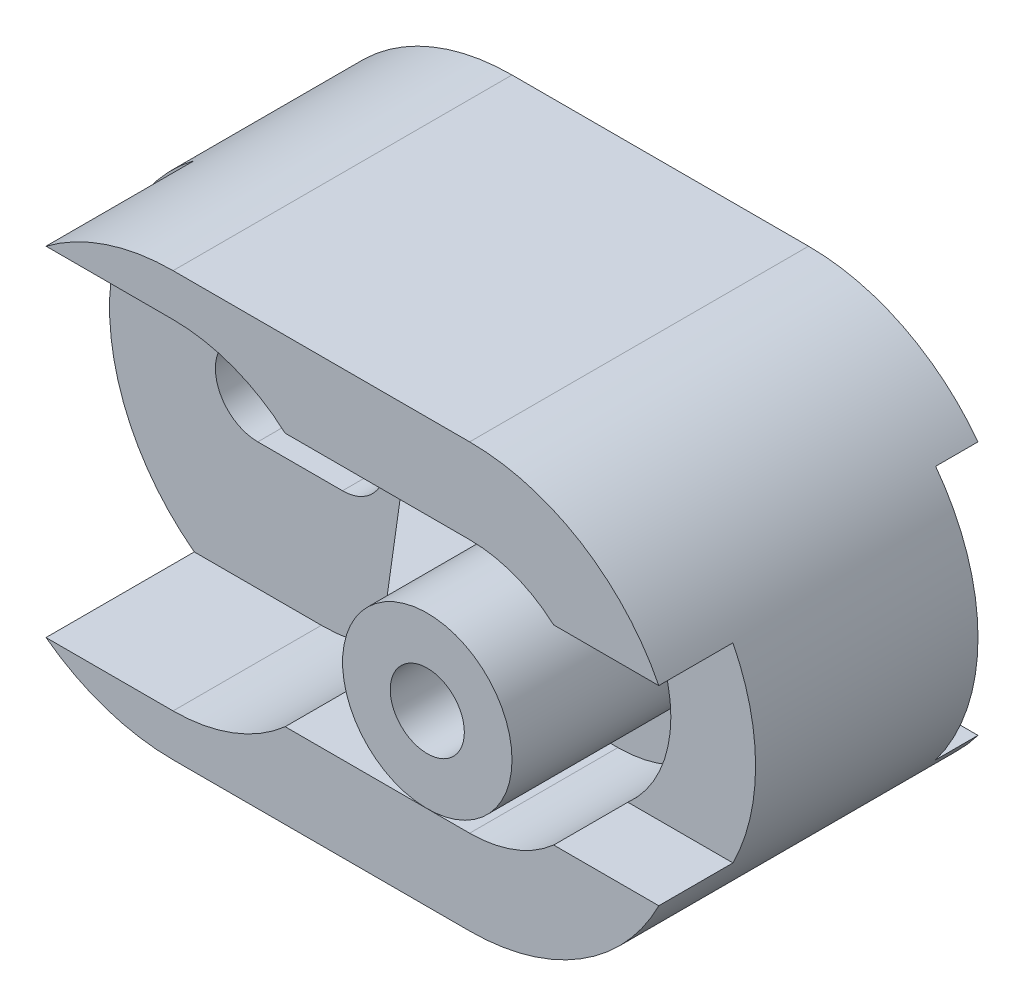
SolidWorks part; units mm, degrees
ref_plane "Front" through (0, 0, 0) normal (0, 0, 1) x (1, 0, 0)
ref_plane "Top" through (0, 0, 0) normal (0, 1, 0) x (1, 0, 0)
ref_plane "Right" through (0, 0, 0) normal (1, 0, 0) x (0, 0, -1)
sketch "Sketch1" plane through (0, 0, 0) normal (0, 0, 1) x (1, 0, 0)
  line L0 (-3.5, 0) -> (3.5, 0) construction
  line L1 (-3.5, 5) -> (3.5, 5)
  line L2 (-3.5, -5) -> (3.5, -5)
  arc A0 (-3.5, 5) -> (-3.5, -5) centre (-3.5, 0) ccw
  arc A1 (3.5, -5) -> (3.5, 5) centre (3.5, 0) ccw
  point P3 (0, 0)
  dimension "D3" = 5
  dimension "D1" = 7
  dimension "D2" = 0
extrude "Boss-Extrude1" add sketch "Sketch1" along normal blind 8
sketch "Sketch2" plane through (0, 0, 0) normal (1, 0, 0) x (0, 0, -1)
  line L0 (0, -5) -> (0, 5) construction
  line L1 (0, 3) -> (-1, 3)
  line L2 (0, 3) -> (0, -3)
  line L3 (0, -3) -> (-1, -3)
  line L4 (-1, 3) -> (-1, -3)
  line L5 (-8, 5) -> (0, 5) construction
  line L6 (-8, -5) -> (0, -5) construction
  dimension "D1" = 1
  dimension "D2" = 2
  dimension "D3" = 2
extrude "Cut-Extrude1" cut sketch "Sketch2" against normal mid plane 18
sketch "Sketch3" plane through (0, 0, 1) normal (0, 0, -1) x (-1, 0, 0)
  line L0 (3.0009, 0) -> (8.5, 0) construction
  line L1 (3.0009, 2) -> (8.5, 2)
  line L2 (3.0009, -2) -> (8.5, -2)
  arc A0 (7.5, -3) -> (7.5, 3) centre (3.5, 0) ccw construction
  arc A1 (3.0009, 2) -> (3.0009, -2) centre (3.0009, 0) ccw
  arc A2 (8.5, -2) -> (8.5, 2) centre (8.5, 0) ccw
  point P5 (5.7505, 0)
  dimension "D1" = 2
extrude "Cut-Extrude2" cut sketch "Sketch3" against normal blind 1
sketch "Sketch4" plane through (0, 0, 8) normal (0, 0, 1) x (1, 0, 0)
  line L0 (-9.1616, 0) -> (-3.5, 0) construction
  line L1 (-9.1616, 4) -> (-3.5, 4)
  line L2 (-9.1616, -4) -> (-3.5, -4)
  line L3 (-3.5, 0) -> (3.5, 0) construction
  line L4 (-3.5, 3) -> (3.5, 3)
  line L5 (-3.5, -3) -> (3.5, -3)
  arc A0 (-9.1616, 4) -> (-9.1616, -4) centre (-9.1616, 0) ccw
  arc A1 (-3.5, -4) -> (-3.5, 4) centre (-3.5, 0) ccw
  arc A2 (-3.5, 3) -> (-3.5, -3) centre (-3.5, 0) ccw
  arc A3 (3.5, -3) -> (3.5, 3) centre (3.5, 0) ccw
  circle A4 centre (3.5, 0) radius 2
  point P3 (-6.3308, 0)
  point P10 (0, 0)
  arc M5 (-3.5, 5) -> (-3.5, -5) centre (-3.5, 0) ccw
  dimension "D1" = 4
  dimension "D4" = 3
  dimension "D5" = 4
  dimension "D2" = 3.5
  dimension "D3" = 7
extrude "Cut-Extrude3" cut sketch "Sketch4" against normal blind 3.5 contours L1 A0 L2 M5 | A2 L4 A1 L1 L2 L5 M5 | L4 A2 L5 A1 | L5 A3 L4 A1
sketch "Sketch5" plane through (0, 0, 0) normal (0, 1, 0) x (1, 0, 0)
  line L0 (1.5, -8) -> (-1.5, -4.5)
  line L1 (1.5, -8) -> (5.5, -8) construction
  line L2 (-1.5, -4.5) -> (1.5, -4.5)
  line L3 (1.5, -4.5) -> (1.5, -8)
  dimension "D1" = 3
  dimension "D2" = 3.5
extrude "Boss-Extrude3" add sketch "Sketch5" along normal mid plane 1 separate body
sketch "Sketch6" plane through (0, 0, 2) normal (0, 0, -1) x (-1, 0, 0)
  line L0 (3.0009, 0) -> (5.0009, 0) construction
  line L1 (3.0009, 1) -> (5.0009, 1)
  line L2 (3.0009, -1) -> (5.0009, -1)
  arc A0 (3.0009, 1) -> (3.0009, -1) centre (3.0009, 0) ccw
  arc A1 (5.0009, -1) -> (5.0009, 1) centre (5.0009, 0) ccw
  point P4 (4.0009, 0)
  dimension "D2" = 1
  dimension "D1" = 2
extrude "Cut-Extrude4" cut sketch "Sketch6" against normal blind 6.0257
sketch "Sketch7" plane through (0, 0, 8) normal (0, 0, 1) x (1, 0, 0)
  line L5 (5.4843, 2.25) -> (7.9651, 2.25)
  line L7 (5.4843, -2.25) -> (7.9651, -2.25)
  line L10 (-3.5, -4) -> (-6.5, -4)
  line L11 (-3.5, -5) -> (3.5, -5)
  line L12 (3.5, 5) -> (-3.5, 5)
  line L13 (-6.5, 4) -> (-3.5, 4)
  line L14 (-0.8542, 3) -> (3.5, 3)
  line L15 (3.5, -3) -> (-0.8542, -3)
  line L16 (-3.5, -4) -> (-6.5, -4)
  line L17 (-3.5, -5) -> (3.5, -5)
  line L18 (3.5, 5) -> (-3.5, 5)
  line L19 (-6.5, 4) -> (-3.5, 4)
  line L20 (-0.8542, 3) -> (3.5, 3)
  line L21 (3.5, -3) -> (-0.8542, -3)
  arc A7 (-6.5, -4) -> (-3.5, -5) centre (-3.5, 0) ccw
  arc A8 (3.5, -5) -> (3.5, 5) centre (3.5, 0) ccw
  arc A9 (-3.5, 5) -> (-6.5, 4) centre (-3.5, 0) ccw
  arc A10 (-0.8542, 3) -> (-3.5, 4) centre (-3.5, 0) ccw
  arc A11 (3.5, -3) -> (3.5, 3) centre (3.5, 0) ccw
  arc A12 (-3.5, -4) -> (-0.8542, -3) centre (-3.5, 0) ccw
  arc A13 (-6.5, -4) -> (-3.5, -5) centre (-3.5, 0) ccw
  arc A14 (3.5, -5) -> (3.5, 5) centre (3.5, 0) ccw
  arc A15 (-3.5, 5) -> (-6.5, 4) centre (-3.5, 0) ccw
  arc A16 (-0.8542, 3) -> (-3.5, 4) centre (-3.5, 0) ccw
  arc A17 (3.5, -3) -> (3.5, 3) centre (3.5, 0) ccw
  arc A18 (-3.5, -4) -> (-0.8542, -3) centre (-3.5, 0) ccw
  arc M18 (3.5, -5) -> (3.5, 5) centre (3.5, 0) ccw
  arc M24 (3.5, 3) -> (3.5, -3) centre (3.5, 0) cw
  dimension "D1" = 0
  dimension "D2" = 2.75
  dimension "D3" = 4.5
extrude "Cut-Extrude5" cut sketch "Sketch7" against normal blind 1.75 contours L7 L5 M24 M18
sketch "Sketch8" plane through (0, 0, 8) normal (0, 0, 1) x (1, 0, 0)
  circle A1 centre (3.5, 0) radius 2
  circle A2 centre (3.5, 0) radius 2
  dimension "D1" = 0
extrude "Boss-Extrude4" add sketch "Sketch8" along normal blind 1
hole_wizard "M2.2x0.45 Tapped Hole1" positions "3DSketch1" profile "Sketch9" tap size "M2.2x0.45" standard "ISO"
sketch3d "3DSketch1"
  line L0 (3.5, 0, 4.5) -> (3.5, 0, 9) construction
  point P0 (3.5, 0, 9)
sketch "Sketch9" plane through (3.5, 0, 9) normal (1, 0, 0) x (0, -1, 0)
  line L0 (0, 0) -> (0, 5.0258)
  line L1 (0, 5.0258) -> (0.875, 4.5)
  line L2 (0.875, 4.5) -> (0.875, 0)
  line L5 (0.875, 0) -> (0, 0)
  line L10 (0, 5.0258) -> (-0.875, 4.5) construction
  line L11 (0, -6.35) -> (0, 107.95) construction
  dimension "Tap Drill Dia." = 1.75
  dimension "Tap Drill Depth" = 4.5
  dimension "Drill Angle" = 118
cosmetic thread "Hole Thread1" parameters "D1"=4, "D2"=2.2
